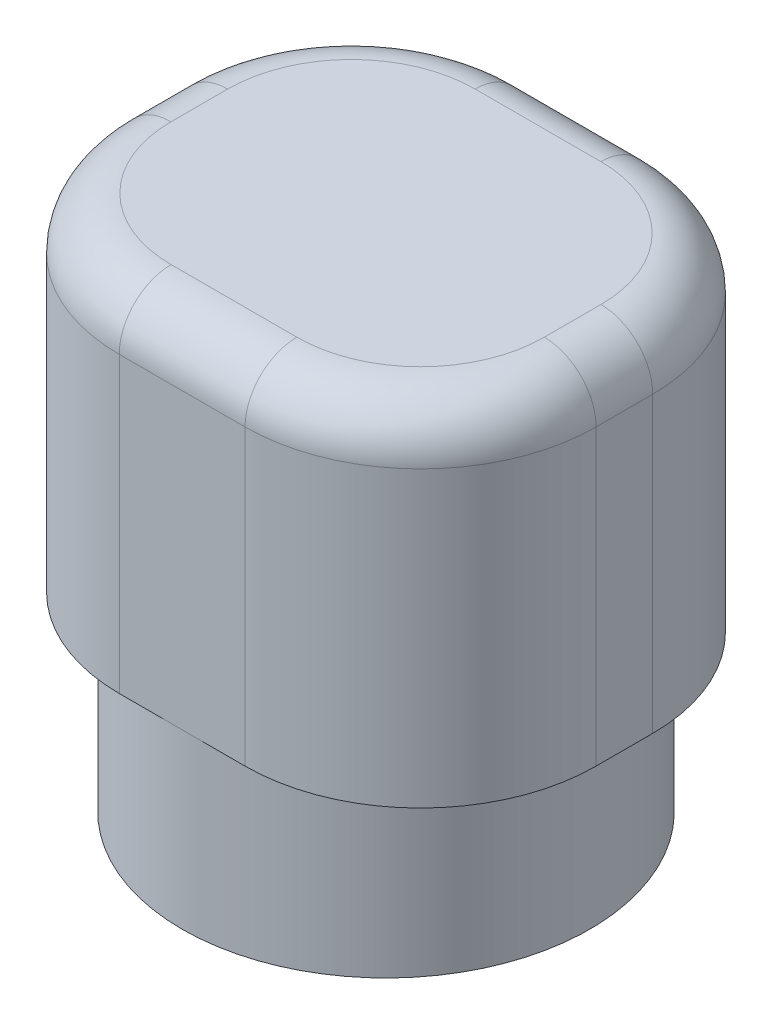
SolidWorks part; units mm, degrees
ref_plane "Front Plane" through (0, 0, 0) normal (0, 0, 1) x (1, 0, 0)
ref_plane "Top Plane" through (0, 0, 0) normal (0, 1, 0) x (1, 0, 0)
ref_plane "Right Plane" through (0, 0, 0) normal (1, 0, 0) x (0, 0, -1)
sketch "Sketch1" plane through (0, 0, 0) normal (0, 1, 0) x (1, 0, 0)
  circle A0 centre (0, 0) radius 2.95
  dimension "D1" = 5.9
extrude "Boss-Extrude1" add sketch "Sketch1" along normal blind 2.5 contours A0
sketch "Sketch2" plane through (0, 0, 0) normal (0, -1, 0) x (1, 0, 0)
  circle A1 centre (0, 0) radius 1.75
  dimension "D1" = 3.5
extrude "Cut-Extrude1" cut sketch "Sketch2" against normal blind 2.5
sketch "Sketch3" plane through (0, 2.5, 0) normal (0, 1, 0) x (1, 0, 0)
  line L1 (-3.45, 2.95) -> (3.45, 2.95)
  line L2 (-3.45, 2.95) -> (-3.45, -2.95)
  line L3 (-3.45, -2.95) -> (3.45, -2.95)
  line L4 (3.45, 2.95) -> (3.45, -2.95)
  line L5 (-3.45, 2.95) -> (3.45, -2.95) construction
  line L6 (-3.45, -2.95) -> (3.45, 2.95) construction
  point P0 (0, 0)
  dimension "D1" = 6.9
  dimension "D2" = 5.9
extrude "Boss-Extrude2" add sketch "Sketch3" along normal blind 5
fillet "Fillet1" radius 2.54 4 edges at (-3.45, 5, -2.95) (3.45, 5, -2.95) (3.45, 5, 2.95) (-3.45, 5, 2.95)
fillet "Fillet2" radius 0.75 8 edges at (3.45, 7.5, 0) (2.7061, 7.5, 2.2061) (2.7061, 7.5, -2.2061) (0, 7.5, -2.95) (-2.7061, 7.5, -2.2061) (-3.45, 7.5, 0) (-2.7061, 7.5, 2.2061) (0, 7.5, 2.95)
